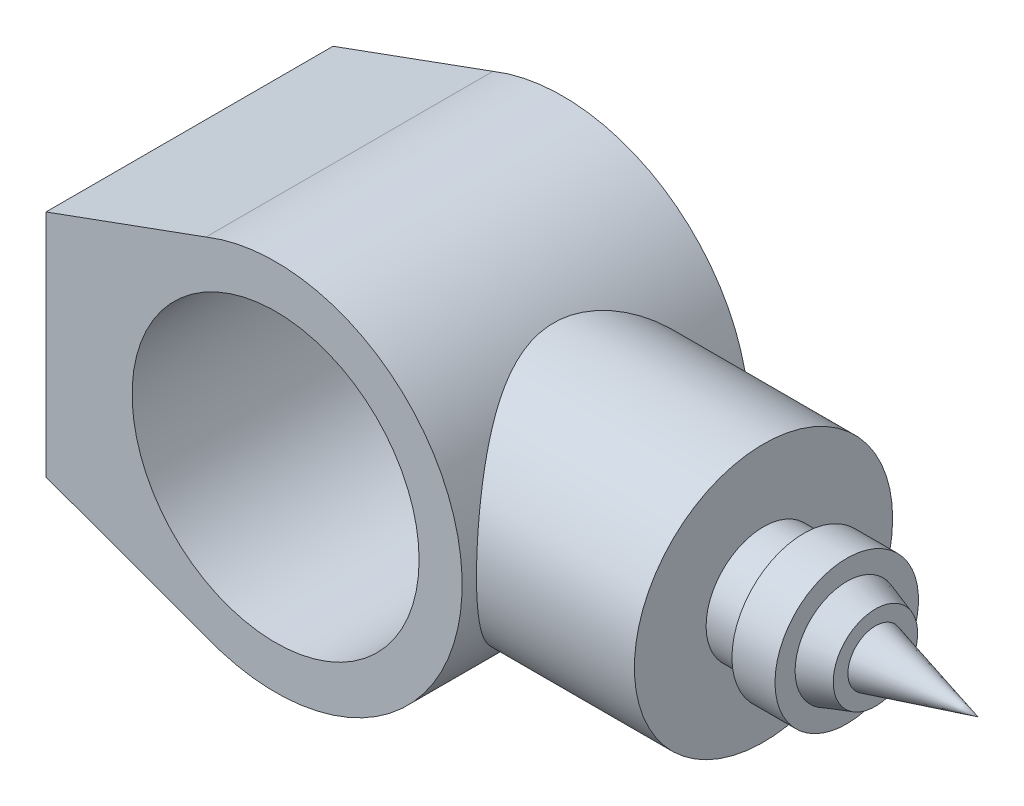
SolidWorks part; units mm, degrees
ref_plane "Front Plane" through (0, 0, 0) normal (0, 0, 1) x (1, 0, 0)
ref_plane "Top Plane" through (0, 0, 0) normal (0, 1, 0) x (1, 0, 0)
ref_plane "Right Plane" through (0, 0, 0) normal (1, 0, 0) x (0, 0, -1)
sketch "Sketch1" plane through (0, 0, 0) normal (0, 0, 1) x (1, 0, 0)
  line L0 (-80, -40) -> (-80, 40)
  line L1 (-80, 40) -> (-24.2587, 60.3035)
  line L2 (-80, -40) -> (-24.2587, -60.3035)
  arc A0 (-24.2587, -60.3035) -> (-24.2587, 60.3035) centre (0, 0) ccw
  circle A1 centre (0, 0) radius 50
  point P7 (-80, 0)
  dimension "D1" = 130
  dimension "D2" = 100
  dimension "D3" = 80
  dimension "D4" = 80
extrude "Boss-Extrude1" add sketch "Sketch1" along normal mid plane 100
ref_plane "Plane1" through (120, 0, 0) normal (1, 0, 0) x (0, 0, -1)
sketch "Sketch2" plane through (120, 0, 0) normal (1, 0, 0) x (0, 0, -1)
  circle A0 centre (0, 0) radius 45
  dimension "D1" = 90
extrude "Boss-Extrude2" add sketch "Sketch2" against normal up to next
sketch "Sketch3" plane through (0, 0, 0) normal (0, 0, 1) x (1, 0, 0)
  line L0 (0, 0) -> (209.6339, 0) construction
  line L1 (120, 0) -> (120, -20)
  line L2 (120, -45) -> (120, 45) construction
  line L3 (120, -20) -> (134, -20)
  line L4 (134, -20) -> (134, -25)
  line L5 (134, -25) -> (149, -25)
  line L6 (149, -25) -> (149, -18)
  line L7 (149, -18) -> (159, -14.7013)
  line L8 (159, -14.7013) -> (159, -9.5884)
  line L9 (159, -9.5884) -> (194.736, 0)
  line L10 (120, 0) -> (194.736, 0)
  dimension "D1" = 20
  dimension "D2" = 14
  dimension "D3" = 5
  dimension "D4" = 15
  dimension "D5" = 7
  dimension "D6" = 10
  dimension "D7" = 37
revolve "Revolve1" add sketch "Sketch3" angle 360 about L0
